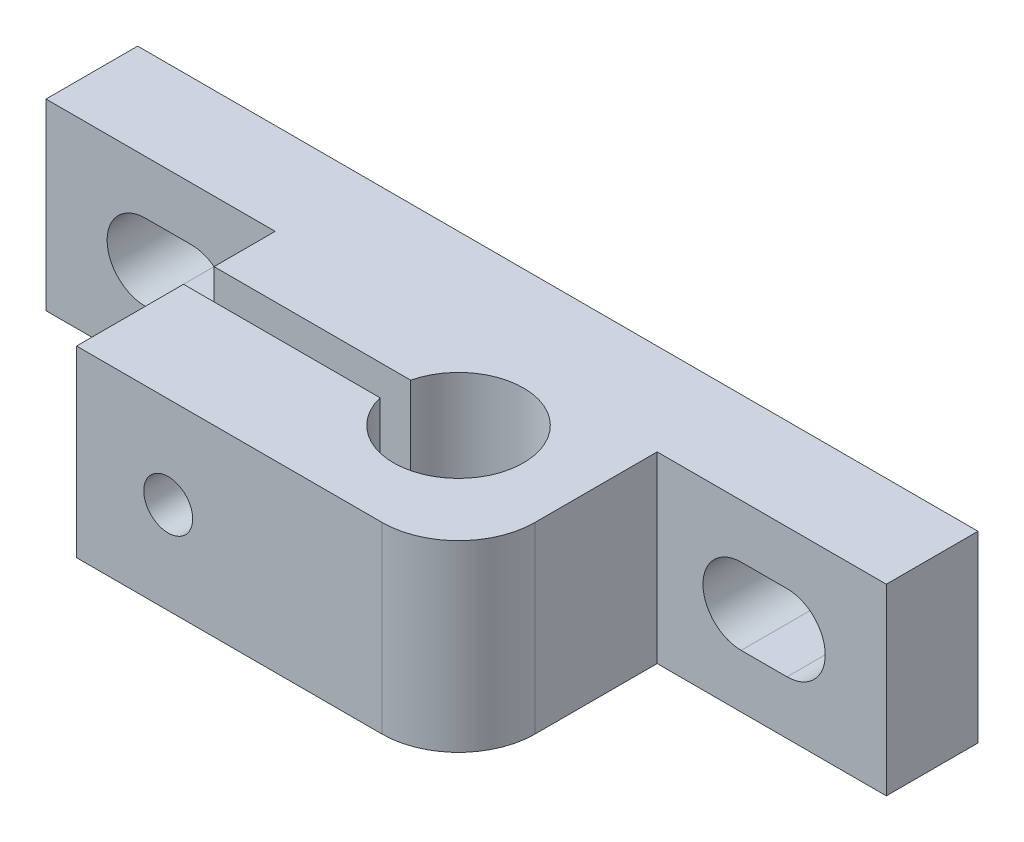
SolidWorks part; units mm, degrees
material "Copper"
ref_plane "Front Plane" through (0, 0, 0) normal (0, 0, 1) x (1, 0, 0)
ref_plane "Top Plane" through (0, 0, 0) normal (0, 1, 0) x (1, 0, 0)
ref_plane "Right Plane" through (0, 0, 0) normal (1, 0, 0) x (0, 0, -1)
sketch "Sketch2" plane through (0, 0, 0) normal (0, 0, 1) x (1, 0, 0)
  line L0 (6.5, 6) -> (9.5, 6) construction
  line L1 (0, 0) -> (55, 0)
  line L2 (0, 0) -> (0, 12)
  line L3 (0, 12) -> (55, 12)
  line L4 (55, 0) -> (55, 12)
  line L5 (27.5, 12) -> (27.5, -3.75) construction
  line L6 (6.5, 8.5) -> (9.5, 8.5)
  line L7 (6.5, 3.5) -> (9.5, 3.5)
  line L8 (48.5, 6) -> (45.5, 6) construction
  line L9 (48.5, 8.5) -> (45.5, 8.5)
  line L10 (48.5, 3.5) -> (45.5, 3.5)
  arc A0 (6.5, 8.5) -> (6.5, 3.5) centre (6.5, 6) ccw
  arc A1 (48.5, 8.5) -> (48.5, 3.5) centre (48.5, 6) cw
  arc A2 (9.5, 3.5) -> (9.5, 8.5) centre (9.5, 6) ccw
  arc A3 (45.5, 3.5) -> (45.5, 8.5) centre (45.5, 6) cw
  point P11 (8, 6)
  point P16 (47, 6)
  dimension "D1" = 6.5
  dimension "D2" = 3
  dimension "D5" = 55
extrude "Boss-Extrude1" add sketch "Sketch2" along normal blind 6
sketch "Sketch3" plane through (0, 0, 6) normal (0, 0, 1) x (1, 0, 0)
  line L0 (0, 0) -> (55, 0) construction
  line L1 (15, 0) -> (40, 0)
  line L2 (15, 0) -> (15, 12)
  line L3 (15, 12) -> (40, 12)
  line L4 (40, 0) -> (40, 12)
  line L5 (55, 12) -> (0, 12) construction
  line L6 (0, 12) -> (0, 0) construction
  line L7 (55, 0) -> (55, 12) construction
  dimension "D1" = 25
  dimension "D2" = 15
  dimension "D3" = 15
extrude "Boss-Extrude2" add sketch "Sketch3" along normal blind 13
fillet "Fillet1" radius 5 1 edges at (40, 6, 19)
sketch "Sketch4" plane through (0, 0, 0) normal (0, -1, 0) x (1, 0, 0)
  line L0 (15, 19) -> (35, 19) construction
  line L1 (40, 14) -> (40, 6) construction
  line L2 (0, 0) -> (55, 0) construction
  line L3 (27.8693, 12) -> (15, 12)
  line L4 (15, 19) -> (15, 6) construction
  line L5 (15, 12) -> (15, 10)
  line L6 (15, 10) -> (27.8693, 10)
  circle A0 centre (32, 11) radius 4.25
  line M4 (15, 19) -> (15, 6)
  dimension "D1" = 8
  dimension "D5" = 8.5
  dimension "D7" = 11
  dimension "D2" = 8
  dimension "D3" = 11
  dimension "D4" = 1
  dimension "D6" = 1
extrude "Cut-Extrude2" cut sketch "Sketch4" against normal blind 30 contours A0 L3 L6 M4 | A0
sketch "Sketch5" plane through (0, 0, 0) normal (0, 0, -1) x (-1, 0, 0)
  line L0 (-55, 12) -> (0, 12) construction
  line L1 (-37.6724, 9.5) -> (-17.1585, 9.5)
  line L2 (-37.6724, 9.5) -> (-37.6724, 2.5)
  line L3 (-37.6724, 2.5) -> (-17.1585, 2.5)
  line L4 (-17.1585, 9.5) -> (-17.1585, 2.5)
  line L5 (0, 0) -> (-55, 0) construction
  line L6 (0, 12) -> (0, 0) construction
  dimension "D1" = 20.5139
  dimension "D2" = 2.5
  dimension "D3" = 2.5
  dimension "D4" = 17.1585
extrude "Cut-Extrude3" cut sketch "Sketch5" against normal blind 5
sketch "Sketch6" plane through (0, 0, 19) normal (0, 0, 1) x (1, 0, 0)
  line L0 (15, 12) -> (15, 0) construction
  line L1 (35, 12) -> (15, 12) construction
  line L2 (15, 0) -> (35, 0) construction
  circle A0 centre (21, 6) radius 1.6
  dimension "D1" = 6
  dimension "D2" = 6
  dimension "D3" = 6
extrude "Cut-Extrude4" cut sketch "Sketch6" against normal blind 11
sketch "Sketch7" plane through (0, 0, 5) normal (0, 0, -1) x (-1, 0, 0)
  line L1 (-17.5359, 6) -> (-19.2679, 9)
  line L2 (-19.2679, 9) -> (-22.7321, 9)
  line L3 (-22.7321, 9) -> (-24.4641, 6)
  line L4 (-24.4641, 6) -> (-22.7321, 3)
  line L5 (-22.7321, 3) -> (-19.2679, 3)
  line L6 (-19.2679, 3) -> (-17.5359, 6)
  circle A0 centre (-21, 6) radius 3 construction
extrude "Cut-Extrude5" cut sketch "Sketch7" against normal blind 3
